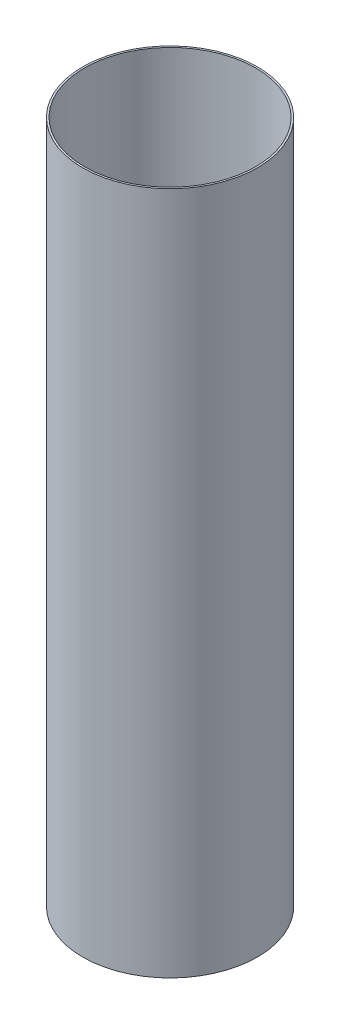
SolidWorks part; units mm, degrees
material "Brown Craft Paper"
ref_plane "Front Plane" through (0, 0, 0) normal (0, 0, 1) x (1, 0, 0)
ref_plane "Top Plane" through (0, 0, 0) normal (0, 1, 0) x (1, 0, 0)
ref_plane "Right Plane" through (0, 0, 0) normal (1, 0, 0) x (0, 0, -1)
sketch "Sketch1" plane through (0, 0, 0) normal (0, 1, 0) x (1, 0, 0)
  circle A0 centre (0, 0) radius 95.4405
  circle A1 centre (0, 0) radius 97.4725
  dimension "D1" = 190.881
  dimension "D2" = 194.945
extrude "Boss-Extrude1" add sketch "Sketch1" along normal blind 762
